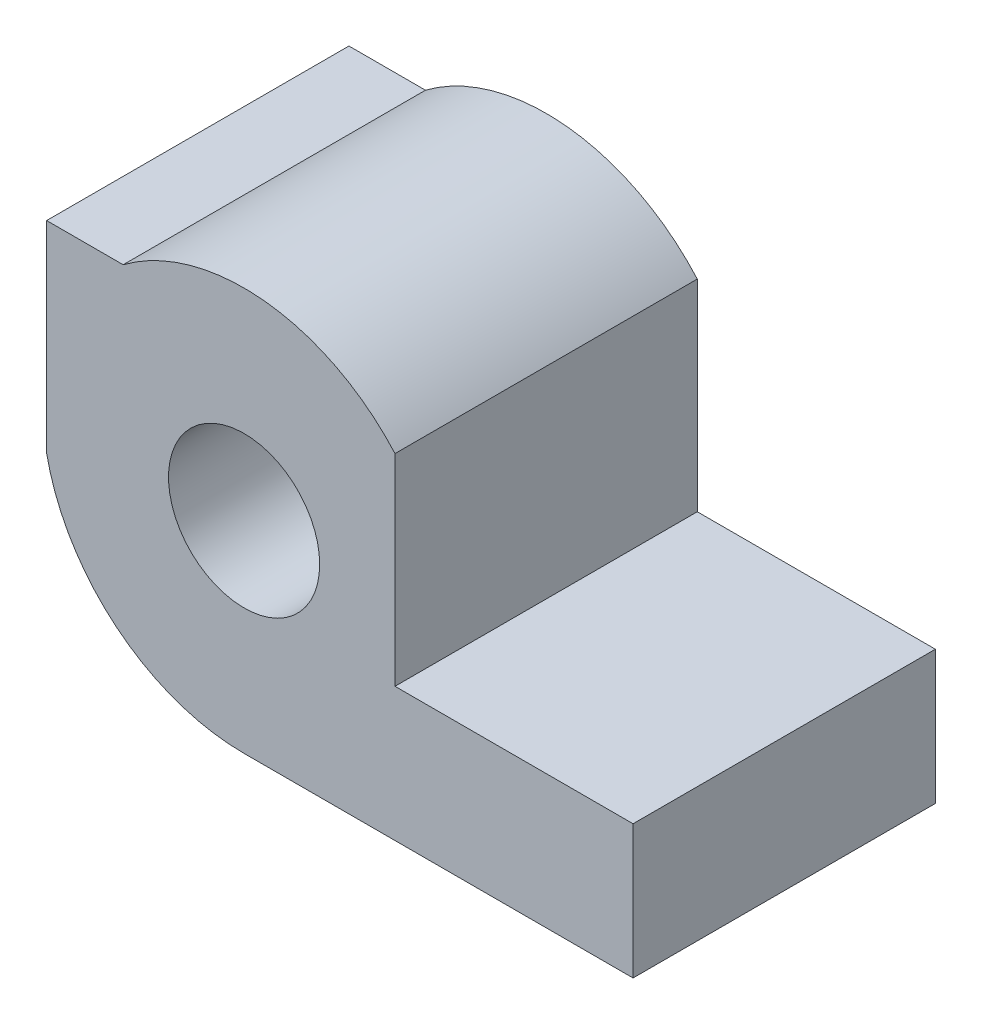
SolidWorks part; units mm, degrees
ref_plane "Front Plane" through (0, 0, 0) normal (0, 0, 1) x (1, 0, 0)
ref_plane "Top Plane" through (0, 0, 0) normal (0, 1, 0) x (1, 0, 0)
ref_plane "Right Plane" through (0, 0, 0) normal (1, 0, 0) x (0, 0, -1)
sketch "Sketch1" plane through (0, 0, 0) normal (0, 0, 1) x (1, 0, 0)
  line L0 (8.3196, -4) -> (0.5996, -4)
  line L1 (-3.3196, 3.2) -> (-3.3196, -0.8)
  line L2 (8.3196, -1.3485) -> (8.3196, -4)
  line L4 (3.5945, 2.6515) -> (3.5945, -1.3485)
  line L6 (3.5945, -1.3485) -> (8.3196, -1.3485)
  line L8 (-3.3196, 3.2) -> (-1.8004, 3.2)
  circle A0 centre (0.5996, 0) radius 1.5
  arc A1 (3.5945, 2.6515) -> (-1.8004, 3.2) centre (0.5996, 0) ccw
  arc A2 (-3.3196, -0.8) -> (0.5996, -4) centre (0.5996, 0) ccw
  dimension "D1" = 3
  dimension "D3" = 0.5996
  dimension "D2" = 4
  dimension "D4" = 3.5945
  dimension "D5" = 8.3196
  dimension "D6" = 1.8004
  dimension "D7" = 3.3196
extrude "Boss-Extrude1" add sketch "Sketch1" along normal blind 6
